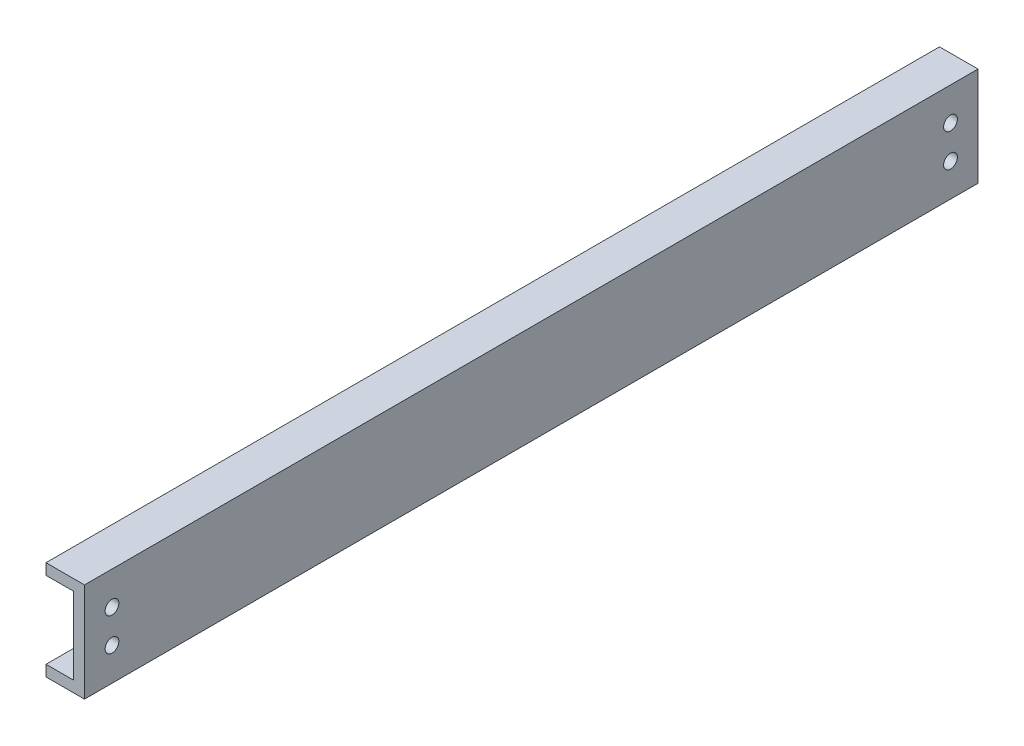
SolidWorks part; units mm, degrees
ref_plane "Front Plane" through (0, 0, 0) normal (0, 0, 1) x (1, 0, 0)
ref_plane "Top Plane" through (0, 0, 0) normal (0, 1, 0) x (1, 0, 0)
ref_plane "Right Plane" through (0, 0, 0) normal (1, 0, 0) x (0, 0, -1)
sketch "Sketch1" plane through (0, 0, 0) normal (0, 0, 1) x (1, 0, 0)
  line L0 (-7, 9.8883) -> (0, 9.8883)
  line L1 (0, 9.8883) -> (0, -8.1117)
  line L2 (0, -8.1117) -> (-7, -8.1117)
  line L3 (-7, 7.8883) -> (-2, 7.8883)
  line L4 (-2, 7.8883) -> (-2, -6.1117)
  line L5 (-2, -6.1117) -> (-7, -6.1117)
  line L6 (-7, 9.8883) -> (-7, 7.8883)
  line L7 (-7, -8.1117) -> (-7, -6.1117)
  dimension "D1" = 18
  dimension "D2" = 7
  dimension "D3" = 7
  dimension "D4" = 2
extrude "Boss-Extrude1" add sketch "Sketch1" against normal blind 162.5
sketch "Sketch2" plane through (0, 0, 0) normal (1, 0, 0) x (0, 0, -1)
  line L0 (0, 0.8883) -> (162.5, 0.8883) construction
  line L3 (0, -8.1117) -> (0, 9.8883) construction
  line L4 (162.5, -8.1117) -> (162.5, 9.8883) construction
  line L5 (162.5, -8.1117) -> (0, -8.1117) construction
  line L6 (2, 9.8883) -> (2, -8.1117) construction
  line L7 (162.5, 9.8883) -> (0, 9.8883) construction
  line L8 (81.25, 9.8883) -> (81.25, -8.1117) construction
  circle A0 centre (5, 3.8883) radius 1.25
  circle A2 centre (5, -2.1117) radius 1.25
  circle A3 centre (157.5, -2.1117) radius 1.25
  circle A4 centre (157.5, 3.8883) radius 1.25
  dimension "D2" = 2.5
  dimension "D1" = 2
  dimension "D3" = 3
  dimension "D4" = 3
extrude "Cut-Extrude1" cut sketch "Sketch2" against normal through all
sketch "Sketch3" plane through (0, -8.1117, 0) normal (0, -1, 0) x (1, 0, 0)
  line L0 (-2, 0) -> (-2, -162.5) construction
  line L3 (-7, -40) -> (0, -40) construction
  line L4 (-7, -162.5) -> (-7, 0) construction
  line L5 (0, -162.5) -> (0, 0) construction
  line L6 (-7, -115) -> (0, -115) construction
  line L7 (-7, 0) -> (0, 0) construction
  line L8 (-7, -162.5) -> (0, -162.5) construction
  line L9 (-4.5, 0) -> (-4.5, -162.5) construction
  circle A4 centre (-4.5, -37) radius 1.25
  circle A5 centre (-4.5, -43) radius 1.25
  circle A6 centre (-4.5, -112) radius 1.25
  circle A7 centre (-4.5, -118) radius 1.25
  dimension "D1" = 2
  dimension "D5" = 3
  dimension "D3" = 2.5
  dimension "D6" = 2.5
  dimension "D2" = 2.5
  dimension "D4" = 75
  dimension "D7" = 3
extrude "Cut-Extrude2" cut sketch "Sketch3" against normal blind 10
